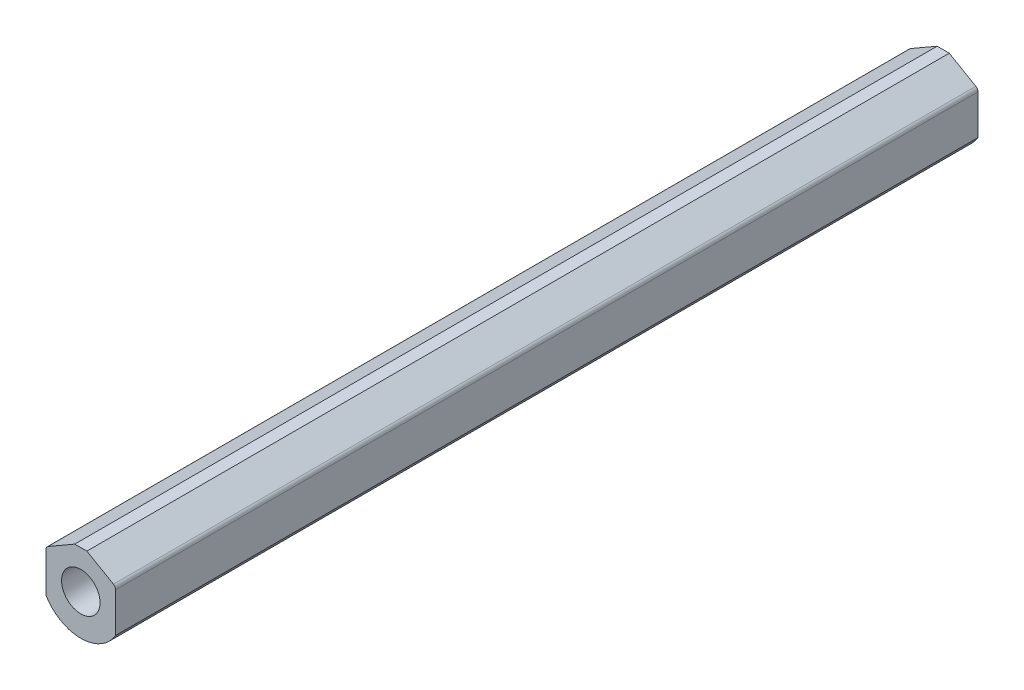
SolidWorks part; units mm, degrees
material "6061 Alloy"
ref_plane "Front Plane" through (0, 0, 0) normal (0, 0, 1) x (1, 0, 0)
ref_plane "Top Plane" through (0, 0, 0) normal (0, 1, 0) x (1, 0, 0)
ref_plane "Right Plane" through (0, 0, 0) normal (1, 0, 0) x (0, 0, -1)
sketch "Sketch1" plane through (0, 0, 0) normal (0, 0, 1) x (1, 0, 0)
  line L0 (-4.287, 26.9748) -> (4.287, 26.9748)
  line L1 (24.5999, 13.4874) -> (24.5999, -14.5388)
  line L2 (0, 0) -> (0, -50.8256) construction
  line L3 (-24.5999, 13.4874) -> (-24.5999, -14.5388)
  line L4 (-4.287, 26.9748) -> (-23.0759, 16.127)
  line L5 (4.287, 26.9748) -> (23.0759, 16.127)
  circle A0 centre (0, 0) radius 13.6144
  arc A1 (-23.0759, 16.127) -> (-24.5999, 13.4874) centre (-21.5519, 13.4874) ccw
  arc A2 (23.0759, 16.127) -> (24.5999, 13.4874) centre (21.5519, 13.4874) cw
  arc A3 (-24.5999, -14.5388) -> (24.5999, -14.5388) centre (0, 0) ccw
  dimension "D1" = 27.2288
  dimension "D2" = 57.15
  dimension "D5" = 3.048
  dimension "D3" = 49.1998
  dimension "D4" = 26.9748
  dimension "D6" = 13.4874
  dimension "D7" = 30
extrude "Extrude1" add sketch "Sketch1" against normal blind 609.6
